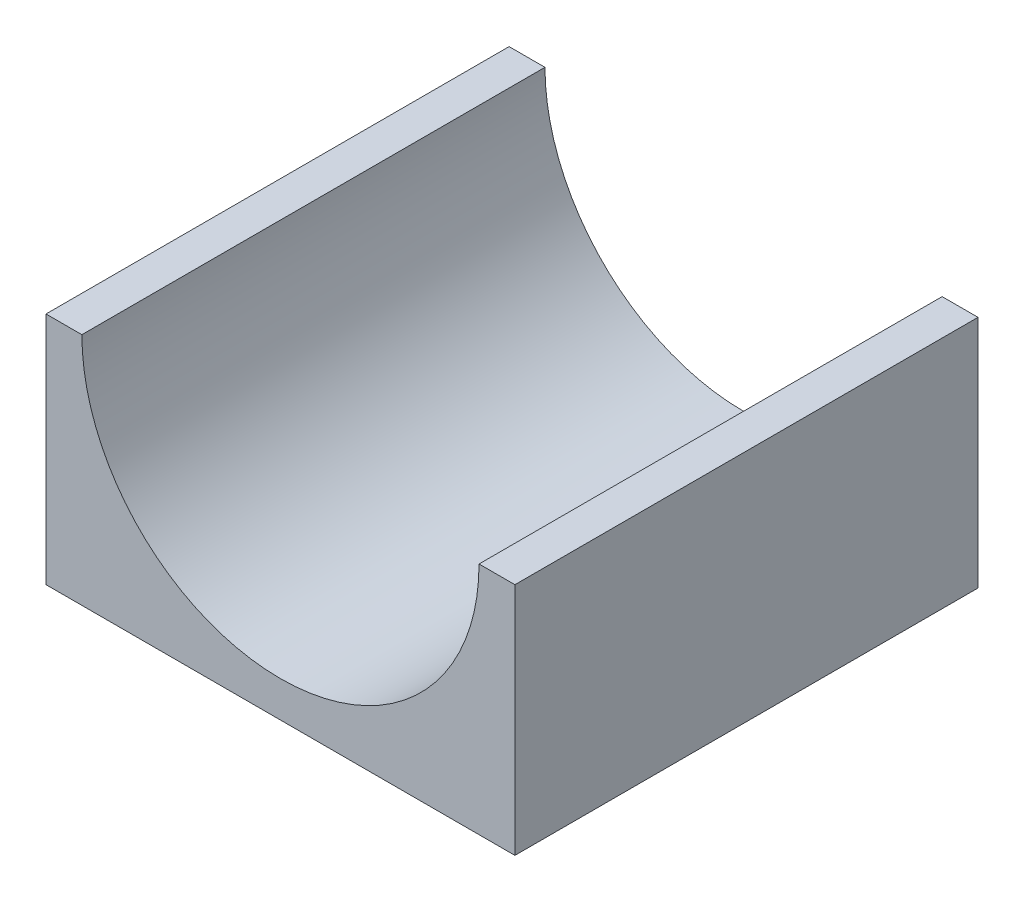
SolidWorks part; units mm, degrees
ref_plane "Front Plane" through (0, 0, 0) normal (0, 0, 1) x (1, 0, 0)
ref_plane "Top Plane" through (0, 0, 0) normal (0, 1, 0) x (1, 0, 0)
ref_plane "Right Plane" through (0, 0, 0) normal (1, 0, 0) x (0, 0, -1)
sketch "Sketch1" plane through (0, 0, 0) normal (0, 0, 1) x (1, 0, 0)
  line L0 (0, 0) -> (0, 65.37)
  line L1 (0, 65.37) -> (10, 65.37)
  line L2 (120.74, 65.37) -> (130.74, 65.37)
  line L3 (130.74, 65.37) -> (130.74, 0)
  line L4 (130.74, 0) -> (0, 0)
  line L5 (65.37, 65.37) -> (65.37, 10) construction
  arc A0 (10, 65.37) -> (120.74, 65.37) centre (65.37, 65.37) ccw
  dimension "D1" = 110.74
  dimension "D2" = 10
  dimension "D3" = 10
extrude "Boss-Extrude1" add sketch "Sketch1" along normal blind 129.12
equation "\"D3@Sketch1\"=\"D2@Sketch1\""
